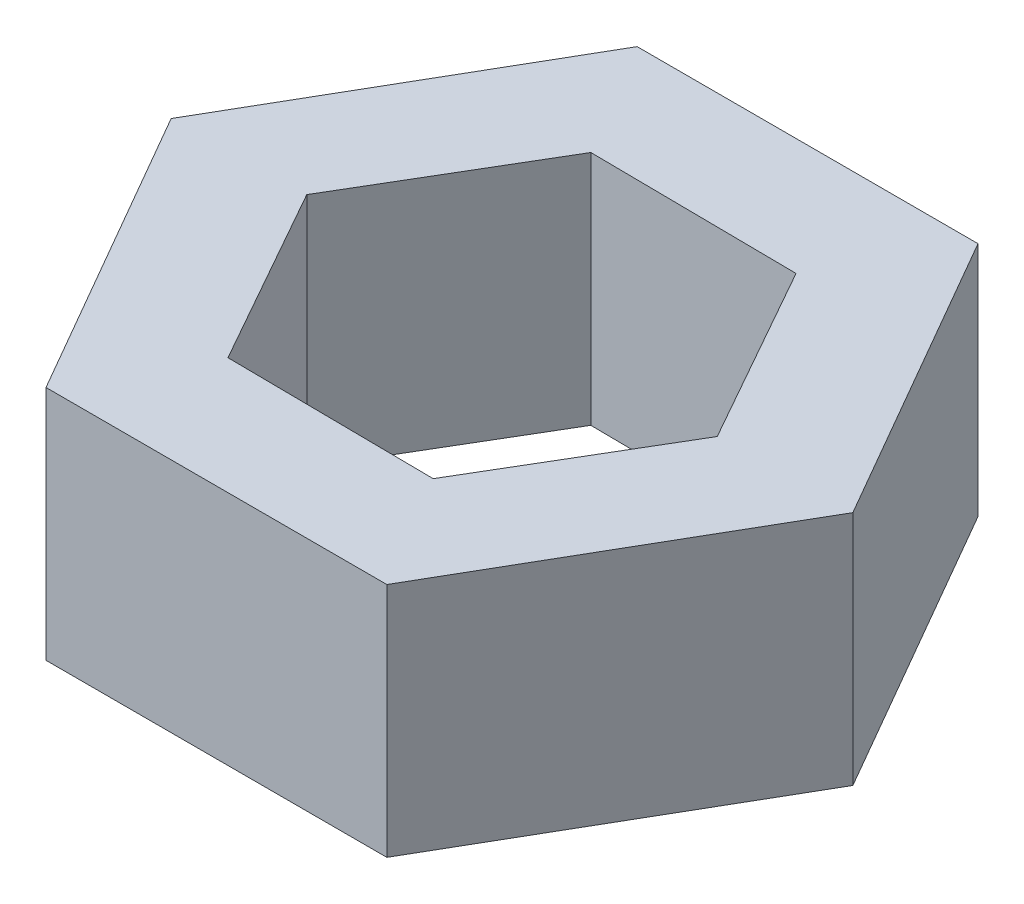
SolidWorks part; units mm, degrees
ref_plane "Front Plane" through (0, 0, 0) normal (0, 0, 1) x (1, 0, 0)
ref_plane "Top Plane" through (0, 0, 0) normal (0, 1, 0) x (1, 0, 0)
ref_plane "Right Plane" through (0, 0, 0) normal (1, 0, 0) x (0, 0, -1)
sketch "Sketch1" plane through (0, 0, 0) normal (0, 1, 0) x (1, 0, 0)
  line L1 (3.6043, -6.2524) -> (7.2169, -0.0048)
  line L2 (7.2169, -0.0048) -> (3.6126, 6.2476)
  line L3 (3.6126, 6.2476) -> (-3.6043, 6.2524)
  line L4 (-3.6043, 6.2524) -> (-7.2169, 0.0048)
  line L5 (-7.2169, 0.0048) -> (-3.6126, -6.2476)
  line L6 (-3.6126, -6.2476) -> (3.6043, -6.2524)
  line L7 (2.1545, -3.8225) -> (4.3876, -0.0454)
  line L8 (4.3876, -0.0454) -> (2.2331, 3.7771)
  line L9 (2.2331, 3.7771) -> (-2.1545, 3.8225)
  line L10 (-2.1545, 3.8225) -> (-4.3876, 0.0454)
  line L11 (-4.3876, 0.0454) -> (-2.2331, -3.7771)
  line L12 (-2.2331, -3.7771) -> (2.1545, -3.8225)
  circle A0 centre (0, 0) radius 6.25 construction
  circle A1 centre (0, 0) radius 3.8 construction
  dimension "D1" = 7.6
  dimension "D2" = 12.5
extrude "Boss-Extrude1" add sketch "Sketch1" along normal blind 5
